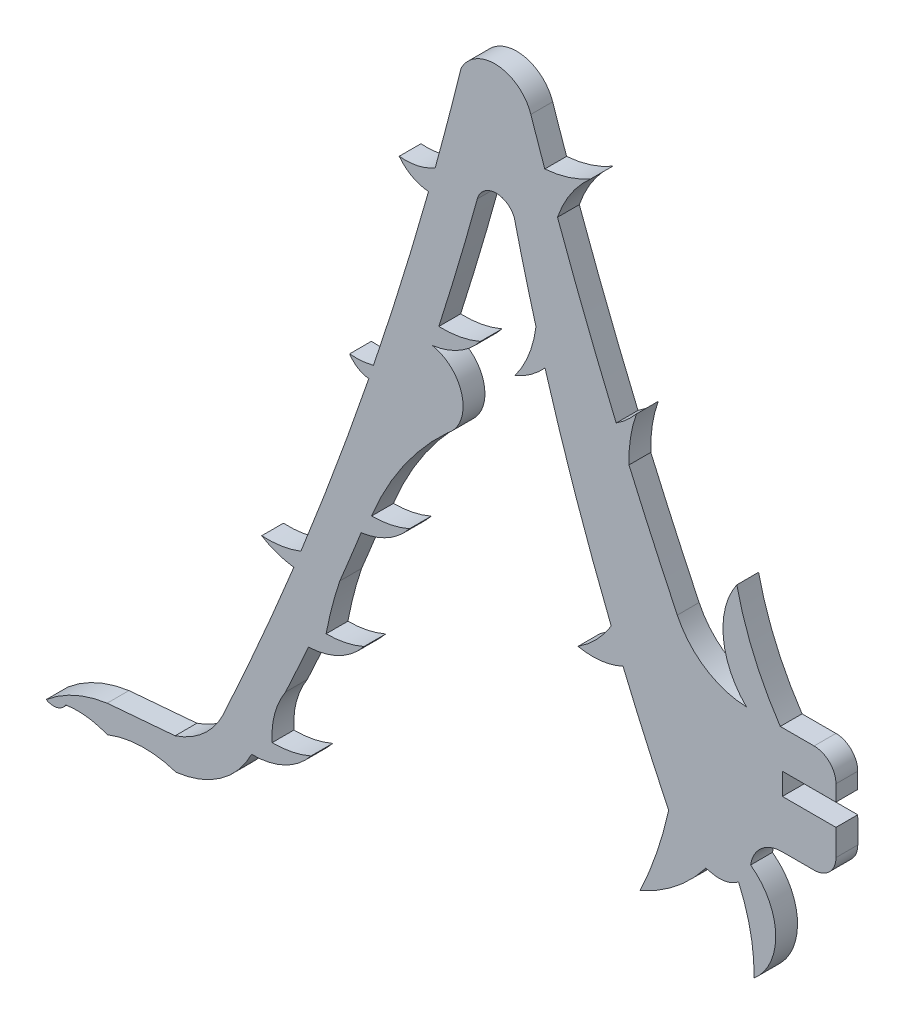
SolidWorks part; units mm, degrees
ref_plane "Front Plane" through (0, 0, 0) normal (0, 0, 1) x (1, 0, 0)
ref_plane "Top Plane" through (0, 0, 0) normal (0, 1, 0) x (1, 0, 0)
ref_plane "Right Plane" through (0, 0, 0) normal (1, 0, 0) x (0, 0, -1)
sketch "Sketch1" plane through (0, 0, 0) normal (0, 0, 1) x (1, 0, 0)
  line L0 (23.8419, -10.5069) -> (26.0682, -10.5059)
  line L1 (27.5942, -8.9781) -> (27.5922, -7.1499)
  line L2 (27.5922, -7.1499) -> (23.8488, -7.1499)
  line L3 (23.8488, -7.1499) -> (23.8468, -5.6239)
  line L4 (23.8468, -5.6239) -> (27.5902, -5.6239)
  line L5 (27.5902, -5.6239) -> (27.5922, -4.5132)
  line L6 (26.0662, -2.9872) -> (23.7007, -2.9877)
  line L7 (-18.5872, -24.6985) -> (-23.3374, -25.0979)
  line L8 (19.1685, -14.3026) -> (18.4955, -14.1663)
  arc A0 (-18.5211, -26.8724) -> (-13.2433, -23.1468) centre (-19.3084, -20.1559) ccw
  arc A1 (-10.8691, -18.1868) -> (-9.2711, -14.6694) centre (-223.2616, 80.4283) ccw
  arc A2 (5.1115, 18.5238) -> (2.5317, 18.3568) centre (3.8505, 17.994) ccw
  arc A3 (5.1115, 18.5238) -> (6.6291, 12.6741) centre (153.6993, 53.9486) ccw
  arc A5 (19.1685, -14.3026) -> (20.7849, -13.8572) centre (19.4299, -12.0954) ccw
  arc A6 (23.8419, -10.5069) -> (21.6302, -12.4093) centre (23.8232, -12.7221) ccw
  arc A7 (26.0682, -10.5059) -> (27.5942, -8.9781) centre (26.0677, -8.9794) ccw
  arc A8 (27.5922, -4.5132) -> (26.0662, -2.9872) centre (26.0662, -4.5132) ccw
  arc A9 (16.5065, 0.1522) -> (21.3353, -2.9882) centre (21.49, 2.5324) ccw
  arc A10 (6.2731, 25.3389) -> (7.2458, 22.5216) centre (220.8075, 97.832) ccw
  arc A11 (6.2731, 25.3389) -> (1.3955, 25.7037) centre (3.7571, 24.4883) ccw
  arc A12 (-15.2378, -21.7595) -> (-10.29, -10.3539) centre (-253.5948, 88.4183) ccw
  arc A13 (-18.5872, -24.6985) -> (-15.2378, -21.7595) centre (-20.3786, -19.279) ccw
  arc A14 (-18.5211, -26.8724) -> (-23.3233, -27.0021) centre (-20.7446, -33.5141) ccw
  arc A15 (-13.2433, -23.1468) -> (-9.095, -21.1749) centre (-13.1688, -17.9543) ccw
  arc A16 (-11.8082, -21.7238) -> (-9.095, -21.1749) centre (-11.7374, -15.0937) ccw
  arc A17 (-9.2711, -14.6694) -> (-5.393, -12.7007) centre (-9.4667, -9.4801) ccw
  arc A18 (-8.0354, -13.25) -> (-5.393, -12.7007) centre (-8.0354, -6.6195) ccw
  arc A19 (-5.5885, -5.9077) -> (-2.213, -3.9824) centre (-6.2867, -0.7618) ccw
  arc A20 (-4.8554, -4.5317) -> (-2.213, -3.9824) centre (-4.8554, 2.0988) ccw
  arc A21 (-0.6034, 7.9107) -> (2.7419, 9.8317) centre (-1.3318, 13.0524) ccw
  arc A22 (-0.1596, 9.2876) -> (2.7419, 9.8317) centre (0.0996, 15.9129) ccw
  arc A23 (-7.0803, -9.5781) -> (-5.5885, -5.9077) centre (-223.2616, 80.4283) ccw
  arc A24 (-0.1596, 9.2876) -> (2.5317, 18.3568) centre (-223.2616, 80.4283) ccw
  arc A25 (-10.8691, -18.1868) -> (-11.8082, -21.7238) centre (-6.106, -21.3445) ccw
  arc A26 (-7.0803, -9.5781) -> (-8.0354, -13.25) centre (18.4648, -18.1823) ccw
  arc A27 (0.471, 3.1757) -> (-4.8554, -4.5317) centre (14.6025, -12.2843) ccw
  arc A28 (0.471, 3.1757) -> (-0.6034, 7.9107) centre (-1.1186, 5.3044) ccw
  arc A29 (5.151, 8.9609) -> (6.6291, 12.6741) centre (-1.1357, 13.6141) ccw
  arc A30 (5.151, 8.9609) -> (7.2609, 10.4856) centre (2.651, 14.6425) ccw
  arc A31 (9.5671, -5.2082) -> (11.8887, -2.8229) centre (5.5195, 1.0538) ccw
  arc A32 (9.5671, -5.2082) -> (12.7123, -4.8383) centre (10.5876, -0.328) ccw
  arc A33 (7.2609, 10.4856) -> (11.8887, -2.8229) centre (153.6993, 53.9486) ccw
  arc A34 (12.7123, -4.8383) -> (15.8996, -11.9641) centre (153.6993, 53.9486) ccw
  arc A35 (13.6537, 10.9043) -> (13.1307, 7.5513) centre (22.1731, 7.8581) ccw
  arc A36 (12.2349, 9.6406) -> (13.6537, 10.9043) centre (8.6365, 15.1094) ccw
  arc A37 (10.4695, 23.5397) -> (8.1352, 20.0455) centre (15.8715, 17.4041) ccw
  arc A38 (7.2458, 22.5216) -> (10.4695, 23.5397) centre (6.6552, 30.0047) ccw
  arc A39 (-2.9266, 18.2058) -> (-0.4115, 18.7664) centre (-2.4984, 22.2074) ccw
  arc A40 (-2.9266, 18.2058) -> (-0.8773, 17.0947) centre (-0.6766, 19.9101) ccw
  arc A41 (-6.3948, 4.5116) -> (-4.7244, 4.6523) centre (-5.9513, 9.2312) ccw
  arc A42 (-6.3948, 4.5116) -> (-5.0532, 3.6818) centre (-4.8424, 5.522) ccw
  arc A43 (-12.5394, -9.5673) -> (-9.7985, -9.1346) centre (-12.1888, -2.8917) ccw
  arc A44 (-12.5394, -9.5673) -> (-10.29, -10.3539) centre (-9.5818, -4.7191) ccw
  arc A45 (13.1307, 7.5513) -> (16.5065, 0.1522) centre (220.8075, 97.832) ccw
  arc A46 (8.1352, 20.0455) -> (12.2349, 9.6406) centre (220.8075, 97.832) ccw
  arc A47 (-0.4115, 18.7664) -> (1.3955, 25.7037) centre (-253.5948, 88.4183) ccw
  arc A48 (-4.7244, 4.6523) -> (-0.8773, 17.0947) centre (-253.5948, 88.4183) ccw
  arc A49 (-9.7985, -9.1346) -> (-5.0532, 3.6818) centre (-253.5948, 88.4183) ccw
  arc A50 (13.8951, -17.8331) -> (15.8996, -11.9641) centre (-10.5606, -6.2038) ccw
  arc A51 (13.8951, -17.8331) -> (18.4955, -14.1663) centre (9.0441, -7.0277) ccw
  arc A52 (21.8719, -19.127) -> (20.7849, -13.8572) centre (9.4738, -18.9374) ccw
  arc A53 (21.8719, -19.127) -> (21.6302, -12.4093) centre (19.1077, -15.8633) ccw
  arc A54 (-23.3374, -25.0979) -> (-27.5942, -27.0073) centre (-22.1584, -33.426) ccw
  arc A55 (-27.5942, -27.0073) -> (-26.2243, -26.6484) centre (-27.0887, -26.1429) ccw
  arc A56 (-23.3233, -27.0021) -> (-26.2243, -26.6484) centre (-25.4158, -32.0912) ccw
  arc A57 (20.6629, 4.0626) -> (23.7007, -2.9877) centre (40.9566, 8.627) ccw
  arc A58 (20.6629, 4.0626) -> (21.3353, -2.9882) centre (25.227, 0.9403) ccw
extrude "Boss-Extrude1" add sketch "Sketch1" along normal blind 1.524
